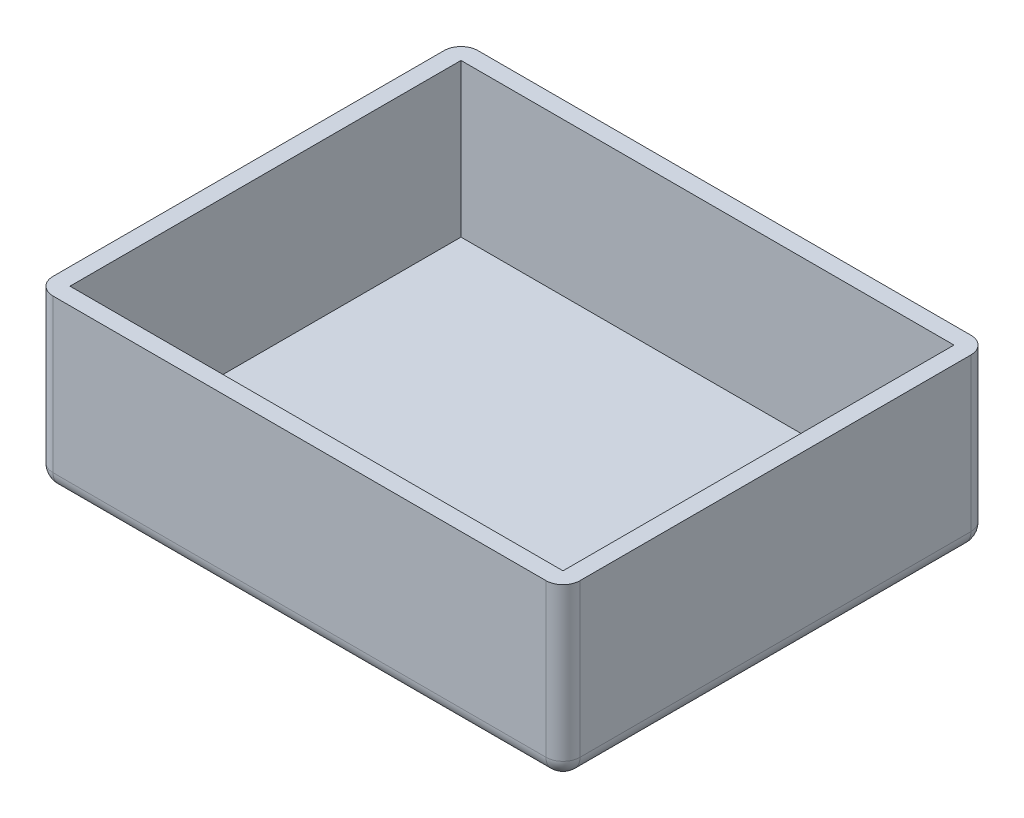
SolidWorks part; units mm, degrees
ref_plane "Plan de face" through (0, 0, 0) normal (0, 0, 1) x (1, 0, 0)
ref_plane "Plan de dessus" through (0, 0, 0) normal (0, 1, 0) x (1, 0, 0)
ref_plane "Plan de droite" through (0, 0, 0) normal (1, 0, 0) x (0, 0, -1)
sketch "Esquisse3" plane through (0, 0, 0) normal (0, 1, 0) x (1, 0, 0)
  line L0 (0, 64.5833) -> (0, -76.7138) construction
  line L2 (-100.8623, 0) -> (88.2826, 0) construction
  line L3 (-77.5, 62.5) -> (77.5, 62.5)
  line L4 (-77.5, 62.5) -> (-77.5, -62.5)
  line L5 (-77.5, -62.5) -> (77.5, -62.5)
  line L6 (77.5, 62.5) -> (77.5, -62.5)
  dimension "D1" = 155
  dimension "D2" = 125
extrude "Boss.-Extru.1" add sketch "Esquisse3" along normal blind 50
sketch "Esquisse4" plane through (0, 50, 0) normal (0, 1, 0) x (1, 0, 0)
  line L0 (0, 35.0722) -> (0, -44.63) construction
  line L1 (-45.197, 0) -> (59.1287, 0) construction
  line L3 (-72.5, 57.5) -> (72.5, 57.5)
  line L4 (-72.5, 57.5) -> (-72.5, -57.5)
  line L5 (-72.5, -57.5) -> (72.5, -57.5)
  line L6 (72.5, 57.5) -> (72.5, -57.5)
  dimension "D1" = 145
  dimension "D2" = 115
extrude "Enlèv. mat.-Extru.1" cut sketch "Esquisse4" against normal blind 45
fillet "Congé1" radius 5 8 edges at (0, 0, 62.5) (77.5, 0, 0) (0, 0, -62.5) (-77.5, 0, 0) (-77.5, 25, -62.5) (-77.5, 25, 62.5) (77.5, 25, -62.5) (77.5, 25, 62.5)
